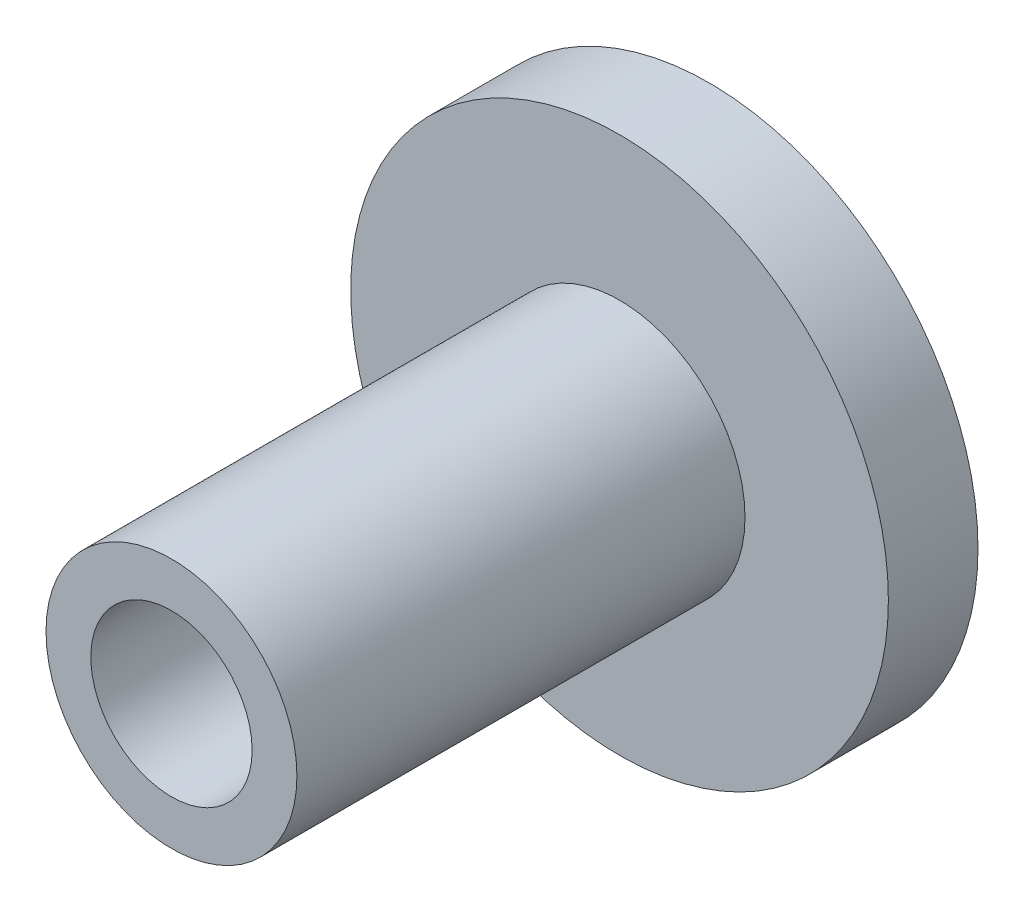
SolidWorks part; units mm, degrees
ref_plane "Front Plane" through (0, 0, 0) normal (0, 0, 1) x (1, 0, 0)
ref_plane "Top Plane" through (0, 0, 0) normal (0, 1, 0) x (1, 0, 0)
ref_plane "Right Plane" through (0, 0, 0) normal (1, 0, 0) x (0, 0, -1)
sketch "Sketch1" plane through (0, 0, 0) normal (0, 0, 1) x (1, 0, 0)
  circle A0 centre (0, 0) radius 15
  dimension "D1" = 30
extrude "Boss-Extrude1" add sketch "Sketch1" along normal blind 5
sketch "Sketch2" plane through (0, 0, 5) normal (0, 0, 1) x (1, 0, 0)
  circle A0 centre (0, 0) radius 7
  dimension "D1" = 14
extrude "Boss-Extrude2" add sketch "Sketch2" along normal blind 25
sketch "Sketch4" plane through (0, 0, 30) normal (0, 0, 1) x (1, 0, 0)
  circle A0 centre (0, 0) radius 4.5
  circle A1 centre (0, 0) radius 7 construction
  dimension "D1" = 9
  dimension "D2" = 2.5
extrude "Cut-Extrude2" cut sketch "Sketch4" against normal blind 20
